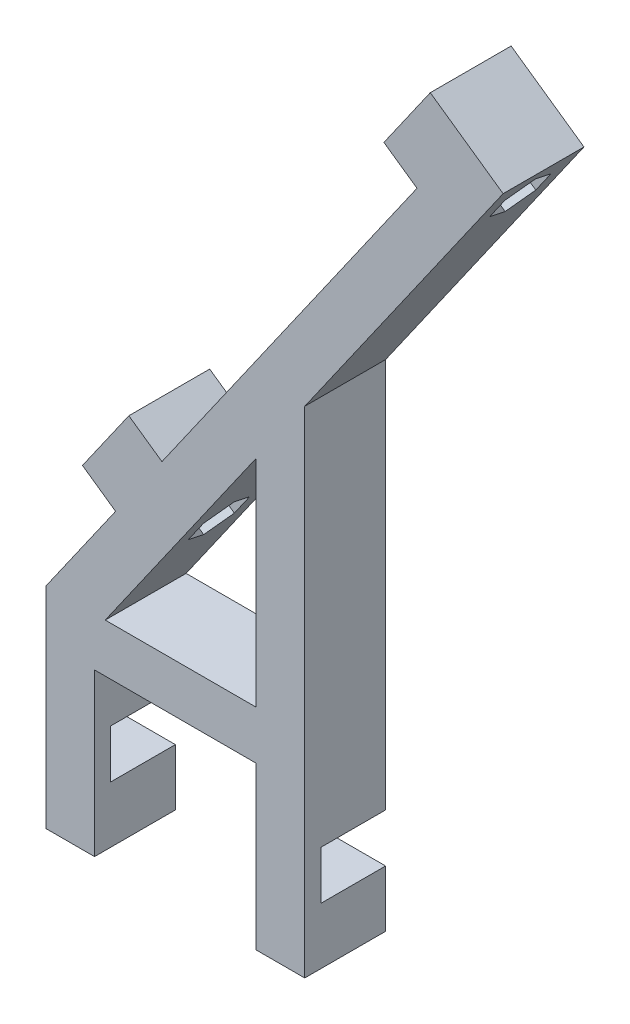
SolidWorks part; units mm, degrees
ref_plane "Front" through (0, 0, 0) normal (0, 0, 1) x (1, 0, 0)
ref_plane "Top" through (0, 0, 0) normal (0, 1, 0) x (1, 0, 0)
ref_plane "Right" through (0, 0, 0) normal (1, 0, 0) x (0, 0, -1)
sketch "Esboço1" plane through (0, 0, 0) normal (0, 0, 1) x (1, 0, 0)
  line L0 (0, 0) -> (0, -26)
  line L1 (0, -26) -> (6, -26)
  line L2 (6, -26) -> (6, -6)
  line L3 (6, -6) -> (26, -6)
  line L4 (32, -26) -> (32, 35.2401)
  line L5 (0, 0) -> (51.6219, 73.7237)
  line L6 (51.6219, 73.7237) -> (56.5368, 70.2822)
  line L7 (56.5368, 70.2822) -> (32, 35.2401)
  line L8 (26, 0) -> (26, 26.6712)
  line L9 (26, 0) -> (7.3246, 0)
  line L10 (7.3246, 0) -> (26, 26.6712)
  line L12 (32, -26) -> (26, -26)
  line L13 (26, -26) -> (26, -6)
  dimension "D1" = 20
  dimension "D2" = 6
  dimension "D3" = 6
  dimension "D4" = 6
  dimension "D5" = 90
  dimension "D6" = 6
  dimension "D7" = 145
  dimension "D8" = 6
  dimension "D9" = 20
extrude "Ressalto-extrusão1" add sketch "Esboço1" along normal blind 10 contours L7 L6 L5 L0 L1 L2 L3 L4 L9 L10 L8
sketch "Esboço3" plane through (0, 0, 0) normal (-1, 0, 0) x (0, 0, 1)
  line L0 (0, 0) -> (0, -26) construction
  line L1 (0, -13) -> (8, -13)
  line L2 (0, -13) -> (0, -19)
  line L3 (0, -19) -> (8, -19)
  line L4 (8, -13) -> (8, -19)
  line L5 (0, -13) -> (8, -19) construction
  line L6 (0, -19) -> (8, -13) construction
  line L8 (10, -26) -> (0, -26) construction
  point P4 (4, -16)
  point P7 (8, -16)
  dimension "D3" = 10
  dimension "D1" = 6
  dimension "D2" = 8
extrude "Corte-extrusão2" cut sketch "Esboço3" against normal through all both and the other way through all
sketch "Esboço2" plane through (0, 0, 0) normal (-0.8192, 0.5736, 0) x (0, 0, 1)
  line L0 (10, 0) -> (0, 0) construction
  line L1 (10, 90) -> (0, 90) construction
  circle A0 centre (5, 85) radius 1.7
  circle A1 centre (5, 20) radius 1.7
  point P6 (5, 0)
  point P10 (5, 90)
  dimension "D1" = 3.4
  dimension "D2" = 65
  dimension "D3" = 5
extrude "Corte-extrusão1" cut sketch "Esboço2" against normal up to next
sketch "Esboço6" plane through (0, 0, 0) normal (-0.8192, 0.5736, 0) x (0, 0, 1)
  line L0 (10, 0) -> (10, 90) construction
  line L1 (0, 80) -> (10, 80)
  line L2 (0, 80) -> (0, 90)
  line L3 (0, 90) -> (10, 90)
  line L4 (10, 80) -> (10, 90)
  line L5 (0, 80) -> (10, 90) construction
  line L6 (0, 90) -> (10, 80) construction
  line L7 (0, 15) -> (10, 15)
  line L8 (0, 15) -> (0, 25)
  line L9 (0, 25) -> (10, 25)
  line L10 (10, 15) -> (10, 25)
  line L11 (0, 15) -> (10, 25) construction
  line L12 (0, 25) -> (10, 15) construction
  circle A0 centre (5, 85) radius 1.7 construction
  circle A1 centre (5, 20) radius 1.7 construction
  circle A2 centre (5, 85) radius 1.7
  circle A3 centre (5, 20) radius 1.7
  point P0 (5, 85)
  point P7 (5, 20)
extrude "Ressalto-extrusão2" add sketch "Esboço6" along normal blind 5
sketch "Esboço7" plane through (4.9149, -3.4415, 0) normal (0.8192, -0.5736, 0) x (0, 0, -1)
  line L1 (-2.15, 83.3546) -> (-2.15, 86.6454)
  line L2 (-2.15, 86.6454) -> (-5, 88.2909)
  line L3 (-5, 88.2909) -> (-7.85, 86.6454)
  line L4 (-7.85, 86.6454) -> (-7.85, 83.3546)
  line L5 (-7.85, 83.3546) -> (-5, 81.7091)
  line L6 (-5, 81.7091) -> (-2.15, 83.3546)
  line L7 (-2.15, 18.3546) -> (-2.15, 21.6454)
  line L8 (-2.15, 21.6454) -> (-5, 23.2909)
  line L9 (-5, 23.2909) -> (-7.85, 21.6454)
  line L10 (-7.85, 21.6454) -> (-7.85, 18.3546)
  line L11 (-7.85, 18.3546) -> (-5, 16.7091)
  line L12 (-5, 16.7091) -> (-2.15, 18.3546)
  circle A0 centre (-5, 85) radius 2.85 construction
  circle A1 centre (-5, 20) radius 2.85 construction
  dimension "D1" = 5.7
extrude "Corte-extrusão5" cut sketch "Esboço7" against normal blind 4
